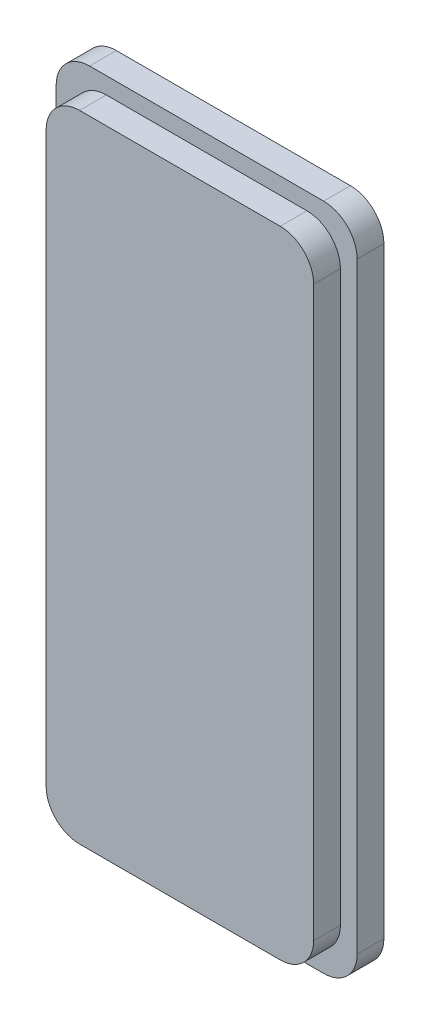
SolidWorks part; units mm, degrees
material "ABS"
ref_plane "前基準面" through (0, 0, 0) normal (0, 0, 1) x (1, 0, 0)
ref_plane "上基準面" through (0, 0, 0) normal (0, 1, 0) x (1, 0, 0)
ref_plane "右基準面" through (0, 0, 0) normal (1, 0, 0) x (0, 0, -1)
sketch "草圖1" plane through (0, 0, 0) normal (0, 0, 1) x (1, 0, 0)
  line L1 (-22.5, -50) -> (22.5, -50)
  line L2 (-22.5, -50) -> (-22.5, 50)
  line L3 (-22.5, 50) -> (22.5, 50)
  line L4 (22.5, -50) -> (22.5, 50)
  line L5 (0, 50) -> (0, -50) construction
  line L6 (-22.5, 0) -> (22.5, 0) construction
  point P0 (0, 0)
  dimension "D1" = 45
  dimension "D2" = 100
extrude "填料-伸長1" add sketch "草圖1" along normal blind 4
sketch "草圖2" plane through (0, 0, 4) normal (0, 0, 1) x (1, 0, 0)
  line L1 (-20, -47.5) -> (20, -47.5)
  line L2 (-20, -47.5) -> (-20, 47.5)
  line L3 (-20, 47.5) -> (20, 47.5)
  line L4 (20, -47.5) -> (20, 47.5)
  line L5 (0, 47.5) -> (0, -47.5) construction
  line L6 (-20, 0) -> (20, 0) construction
  point P0 (0, 0)
  dimension "D1" = 40
  dimension "D2" = 95
extrude "填料-伸長2" add sketch "草圖2" along normal blind 4
fillet "圓角1" radius 5 8 edges at (22.5, -50, 2) (-22.5, -50, 2) (22.5, 50, 2) (-22.5, 50, 2) (-20, 47.5, 6) (20, 47.5, 6) (20, -47.5, 6) (-20, -47.5, 6)
